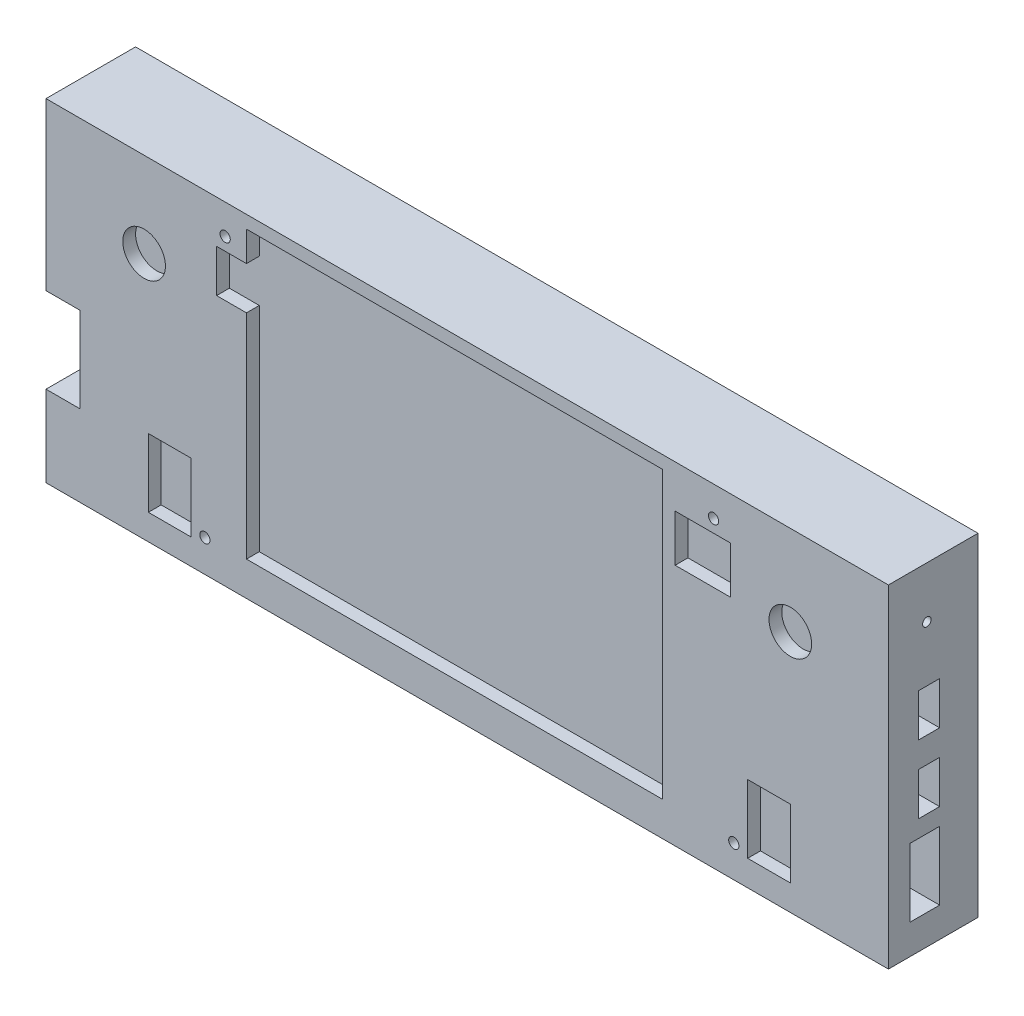
SolidWorks part; units mm, degrees
ref_plane "Front Plane" through (0, 0, 0) normal (0, 0, 1) x (1, 0, 0)
ref_plane "Top Plane" through (0, 0, 0) normal (0, 1, 0) x (1, 0, 0)
ref_plane "Right Plane" through (0, 0, 0) normal (1, 0, 0) x (0, 0, -1)
sketch "Sketch1" plane through (0, 0, 0) normal (0, 0, 1) x (1, 0, 0)
  line L0 (37.25, 7.5) -> (161.25, 7.5) construction
  line L1 (0, 0) -> (197.5, 0)
  line L2 (0, 0) -> (0, 19)
  line L4 (197.5, 0) -> (197.5, 78)
  line L5 (42, 71) -> (156.5, 71) construction
  line L6 (47, 75) -> (47, 68)
  line L7 (0, 39) -> (8, 39)
  line L9 (0, 19) -> (8, 19)
  line L10 (8, 39) -> (8, 19)
  line L11 (47, 75) -> (144.5, 75)
  line L13 (47, 8) -> (144.5, 8)
  line L14 (144.5, 75) -> (144.5, 8)
  line L19 (0, 39) -> (0, 78)
  line L20 (0, 78) -> (197.5, 78)
  line L21 (47, 58) -> (47, 8)
  line L22 (47, 68) -> (40, 68)
  line L24 (47, 58) -> (40, 58)
  line L25 (40, 68) -> (40, 58)
  line L26 (147.5, 68) -> (160.5, 68)
  line L27 (147.5, 68) -> (147.5, 57)
  line L28 (147.5, 57) -> (160.5, 57)
  line L29 (160.5, 68) -> (160.5, 57)
  line L30 (174.5, 22) -> (164.5, 22)
  line L31 (174.5, 22) -> (174.5, 6)
  line L32 (174.5, 6) -> (164.5, 6)
  line L33 (164.5, 22) -> (164.5, 6)
  line L34 (24, 22) -> (34, 22)
  line L35 (24, 22) -> (24, 6)
  line L36 (24, 6) -> (34, 6)
  line L37 (34, 22) -> (34, 6)
  circle A0 centre (37.25, 7.5) radius 1.2
  circle A1 centre (161.25, 7.5) radius 1.2
  circle A2 centre (156.5, 71) radius 1.2
  circle A3 centre (42, 71) radius 1.2
  circle A4 centre (23, 58) radius 5
  circle A5 centre (174.5, 57) radius 5
  point P13 (99.25, 7.5)
  point P14 (99.25, 71)
  dimension "D6" = 2.4
  dimension "D11" = 10
  dimension "D36" = 10
  dimension "D1" = 197.5
  dimension "D2" = 78
  dimension "D3" = 124
  dimension "D4" = 114.5
  dimension "D5" = 63.5
  dimension "D7" = 8
  dimension "D8" = 42
  dimension "D9" = 7.5
  dimension "D10" = 23
  dimension "D12" = 39
  dimension "D13" = 19
  dimension "D14" = 10
  dimension "D15" = 10
  dimension "D16" = 24
  dimension "D17" = 10
  dimension "D18" = 6
  dimension "D19" = 16
  dimension "D20" = 8
  dimension "D21" = 20
  dimension "D22" = 7
  dimension "D23" = 3
  dimension "D24" = 47
  dimension "D25" = 23
  dimension "D26" = 10
  dimension "D27" = 6
  dimension "D28" = 16
  dimension "D29" = 53
  dimension "D30" = 3
  dimension "D31" = 13
  dimension "D32" = 10
  dimension "D33" = 21
  dimension "D34" = 23
  dimension "D35" = 21
extrude "Boss-Extrude2" add sketch "Sketch1" along normal blind 3
sketch "Sketch2" plane through (0, 0, 0) normal (0, 0, -1) x (-1, 0, 0)
  line L1 (-197.5, 78) -> (0, 78)
  line L2 (-197.5, 78) -> (-197.5, 0)
  line L3 (-197.5, 0) -> (0, 0)
  line L4 (0, 78) -> (0, 0)
extrude "Boss-Extrude3" add sketch "Sketch2" along normal blind 18
sketch "Sketch3" plane through (0, 0, -18) normal (0, 0, -1) x (-1, 0, 0)
  line L0 (-194.5, 75) -> (-194.5, 3)
  line L1 (-194.5, 3) -> (-3, 3)
  line L2 (-3, 3) -> (-3, 75)
  line L3 (-3, 75) -> (-194.5, 75)
  line L4 (-197.5, 78) -> (-197.5, 0)
  line L5 (-197.5, 0) -> (0, 0)
  line L6 (0, 0) -> (0, 78)
  line L7 (0, 78) -> (-197.5, 78)
  line L8 (-197.5, 78) -> (-197.5, 0) construction
  line L9 (-197.5, 0) -> (0, 0) construction
  line L10 (0, 0) -> (0, 78) construction
  line L11 (0, 78) -> (-197.5, 78) construction
  dimension "D1" = 0
  dimension "D2" = 3
extrude "Cut-Extrude1" cut sketch "Sketch3" against normal blind 1
sketch "Sketch4" plane through (0, 0, -17) normal (0, 0, -1) x (-1, 0, 0)
  line L0 (-3, 75) -> (-194.5, 75) construction
  line L1 (-187.5, 70) -> (-10, 70)
  line L2 (-187.5, 70) -> (-187.5, 15)
  line L3 (-187.5, 15) -> (-10, 15)
  line L4 (-10, 70) -> (-10, 15)
  line L5 (-3, 3) -> (-3, 75) construction
  line L6 (-194.5, 75) -> (-194.5, 3) construction
  line L7 (-194.5, 3) -> (-3, 3) construction
  dimension "D1" = 5
  dimension "D2" = 7
  dimension "D3" = 7
  dimension "D4" = 12
extrude "Cut-Extrude2" cut sketch "Sketch4" against normal blind 1
sketch "Sketch5" plane through (0, 0, 0) normal (-1, 0, 0) x (0, 0, 1)
  line L1 (3, 39) -> (-8, 39)
  line L2 (3, 39) -> (3, 19)
  line L3 (3, 19) -> (-8, 19)
  line L4 (-8, 39) -> (-8, 19)
  dimension "D1" = 11
extrude "Cut-Extrude3" cut sketch "Sketch5" against normal up to surface (8 mm away) up to face at (8, 29, 1.5)
sketch "Sketch6" plane through (197.5, 0, 0) normal (1, 0, 0) x (0, 0, -1)
  line L0 (-3, 0) -> (-3, 78) construction
  line L1 (2, 23) -> (9, 23)
  line L2 (2, 23) -> (2, 7)
  line L3 (2, 7) -> (9, 7)
  line L4 (9, 23) -> (9, 7)
  line L5 (4, 37) -> (9, 37)
  line L6 (4, 37) -> (4, 27)
  line L7 (4, 27) -> (9, 27)
  line L8 (9, 37) -> (9, 27)
  line L9 (4, 53) -> (9, 53)
  line L10 (4, 53) -> (4, 43)
  line L11 (4, 43) -> (9, 43)
  line L12 (9, 53) -> (9, 43)
  line L13 (-3, 0) -> (18, 0) construction
  line L14 (-3, 78) -> (18, 78) construction
  circle A0 centre (6, 66) radius 1
  dimension "D13" = 12
  dimension "D15" = 2
  dimension "D1" = 5
  dimension "D2" = 7
  dimension "D3" = 7
  dimension "D4" = 16
  dimension "D5" = 7
  dimension "D6" = 5
  dimension "D7" = 10
  dimension "D8" = 7
  dimension "D9" = 10
  dimension "D10" = 5
  dimension "D11" = 27
  dimension "D12" = 43
  dimension "D14" = 9
extrude "Cut-Extrude4" cut sketch "Sketch6" against normal blind 10
